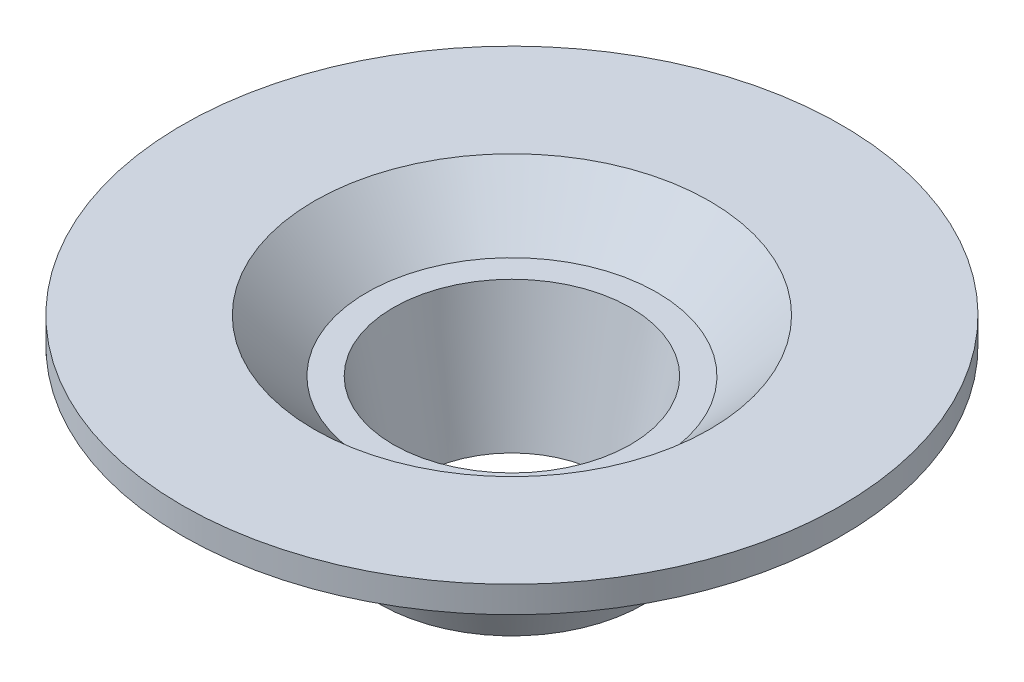
SolidWorks part; units mm, degrees
ref_plane "Front Plane" through (0, 0, 0) normal (0, 0, 1) x (1, 0, 0)
ref_plane "Top Plane" through (0, 0, 0) normal (0, 1, 0) x (1, 0, 0)
ref_plane "Right Plane" through (0, 0, 0) normal (1, 0, 0) x (0, 0, -1)
sketch "Sketch1" plane through (0, 0, 0) normal (1, 0, 0) x (0, 0, -1)
  line L0 (0, 0) -> (0, -8.135) construction
  line L1 (3.5, -8.135) -> (4.5, -3.135)
  line L2 (4.5, -3.135) -> (5.5, -3.135)
  line L3 (5.5, -3.135) -> (7.5, -1.135)
  line L4 (7.5, -1.135) -> (12.5, -1.135)
  line L5 (12.5, -1.135) -> (12.5, -2.135)
  line L6 (12.5, -2.135) -> (10.5, -2.135)
  line L7 (10.5, -2.135) -> (8.5, -4.135)
  line L8 (8.5, -4.135) -> (6.5, -4.135)
  line L9 (6.5, -4.135) -> (5, -8.135)
  line L10 (5, -8.135) -> (3.5, -8.135)
  point P10 (0, 0)
  point P16 (-2.5225, 0.7232)
  point P17 (7.3619, -3.3818)
  point P18 (7.4298, -3.0494)
  dimension "D1" = 3.5
  dimension "D2" = 1.5
  dimension "D3" = 6.5
  dimension "D4" = 5
  dimension "D5" = 4
  dimension "D6" = 12.5
  dimension "D7" = 1
  dimension "D8" = 2
  dimension "D9" = 2
  dimension "D10" = 2
  dimension "D11" = 4.5
  dimension "D12" = 1
revolve "Revolve1" add sketch "Sketch1" angle 360 about L0
